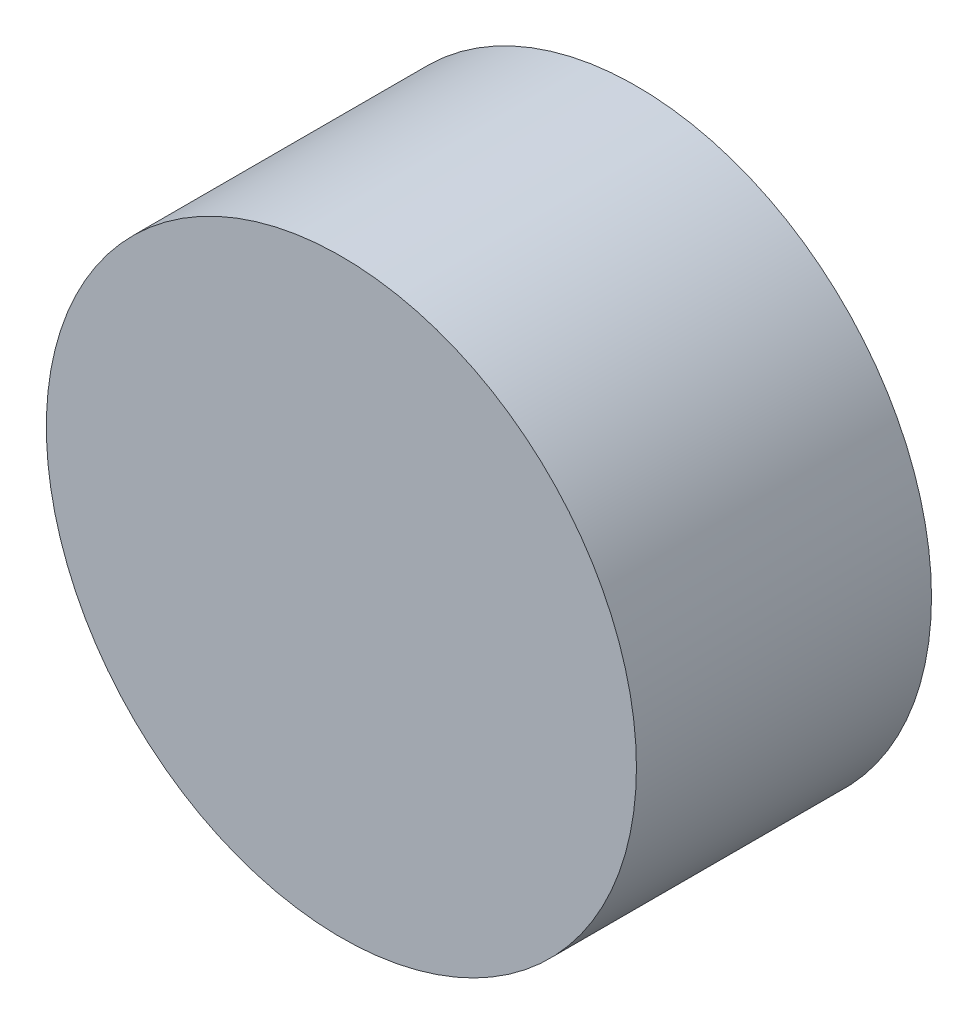
SolidWorks part; units mm, degrees
ref_plane "Front Plane" through (0, 0, 0) normal (0, 0, 1) x (1, 0, 0)
ref_plane "Top Plane" through (0, 0, 0) normal (0, 1, 0) x (1, 0, 0)
ref_plane "Right Plane" through (0, 0, 0) normal (1, 0, 0) x (0, 0, -1)
sketch "Sketch1" plane through (0, 0, 0) normal (0, 0, 1) x (1, 0, 0)
  circle A0 centre (-26.1309, 18.7712) radius 10
  dimension "D1" = 20
extrude "Boss-Extrude1" add sketch "Sketch1" along normal blind 10
